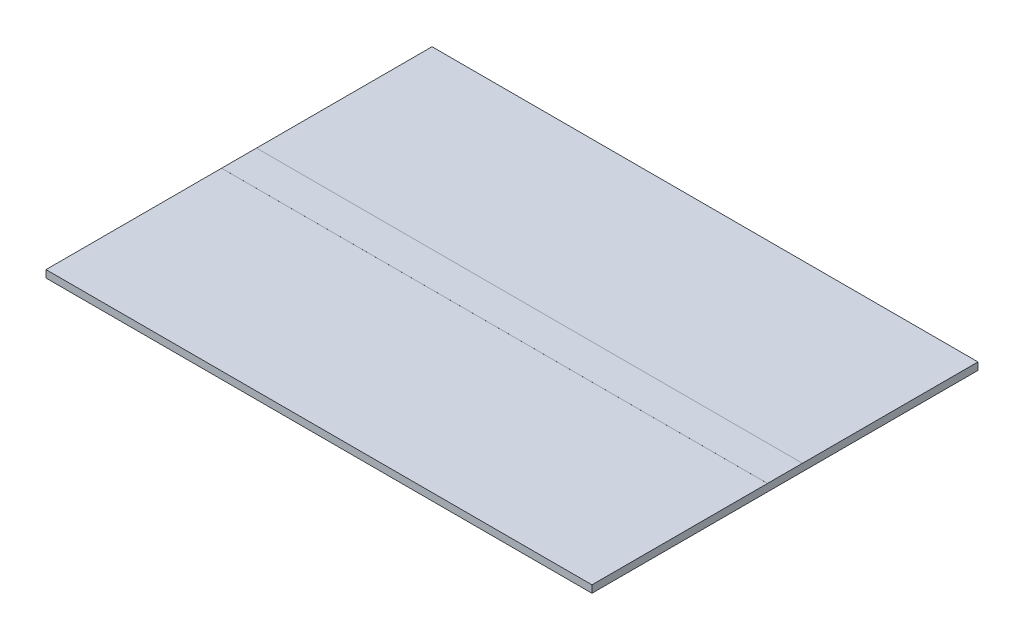
SolidWorks part; units mm, degrees
ref_plane "Front Plane" through (0, 0, 0) normal (0, 0, 1) x (1, 0, 0)
ref_plane "Top Plane" through (0, 0, 0) normal (0, 1, 0) x (1, 0, 0)
ref_plane "Right Plane" through (0, 0, 0) normal (1, 0, 0) x (0, 0, -1)
sketch "Sketch1" plane through (0, 0, 0) normal (0, 1, 0) x (1, 0, 0)
  line L1 (-127.3659, 71.2576) -> (169.6341, 71.2576)
  line L2 (-127.3659, 71.2576) -> (-127.3659, -138.7424)
  line L3 (-127.3659, -138.7424) -> (169.6341, -138.7424)
  line L4 (169.6341, 71.2576) -> (169.6341, -138.7424)
  dimension "D1" = 297
  dimension "D2" = 210
extrude "Boss-Extrude1" add sketch "Sketch1" along normal blind 4
sketch "Sketch2" plane through (0, 4, 0) normal (0, 1, 0) x (1, 0, 0)
  line L0 (-127.3659, 71.2576) -> (-127.3659, -138.7424) construction
  line L1 (-127.3659, -24.2424) -> (169.6341, -24.2424)
  line L2 (-127.3659, -24.2424) -> (-127.3659, -43.2424)
  line L3 (-127.3659, -43.2424) -> (169.6341, -43.2424)
  line L4 (169.6341, -24.2424) -> (169.6341, -43.2424)
  line L5 (169.6341, -138.7424) -> (169.6341, 71.2576) construction
  line L6 (169.6341, 71.2576) -> (-127.3659, 71.2576) construction
  dimension "D1" = 19
  dimension "D2" = 95.5
extrude "Boss-Extrude2" add sketch "Sketch2" along normal blind 0.01
